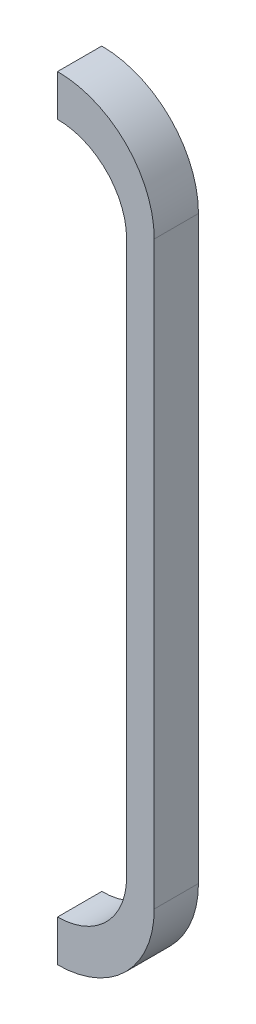
SolidWorks part; units mm, degrees
ref_plane "Front Plane" through (0, 0, 0) normal (0, 0, 1) x (1, 0, 0)
ref_plane "Top Plane" through (0, 0, 0) normal (0, 1, 0) x (1, 0, 0)
ref_plane "Right Plane" through (0, 0, 0) normal (1, 0, 0) x (0, 0, -1)
sketch "Sketch1" plane through (0, 0, 0) normal (0, 0, 1) x (1, 0, 0)
  line L1 (13.5, 10.5) -> (13.5, -10.5) construction
  line L4 (13.5, 10.5) -> (13.5, -10.5)
  line L6 (12.5, -10) -> (12.5, 10) construction
  line L18 (12.5, -10) -> (12.5, 10)
  line L34 (10, 12.5) -> (10, 14)
  line L35 (10, -14) -> (10, -12.5)
  arc A0 (10, -14) -> (13.5, -10.5) centre (10, -10.5) ccw construction
  arc A1 (13.5, 10.5) -> (10, 14) centre (10, 10.5) ccw construction
  arc A2 (10, -14) -> (13.5, -10.5) centre (10, -10.5) ccw
  arc A3 (13.5, 10.5) -> (10, 14) centre (10, 10.5) ccw
  arc A4 (10, -12.5) -> (12.5, -10) centre (10, -10) ccw construction
  arc A15 (12.5, 10) -> (10, 12.5) centre (10, 10) ccw construction
  arc A16 (10, -12.5) -> (12.5, -10) centre (10, -10) ccw
  arc A27 (12.5, 10) -> (10, 12.5) centre (10, 10) ccw
extrude "Boss-Extrude1" add sketch "Sketch1" along normal blind 1.6
